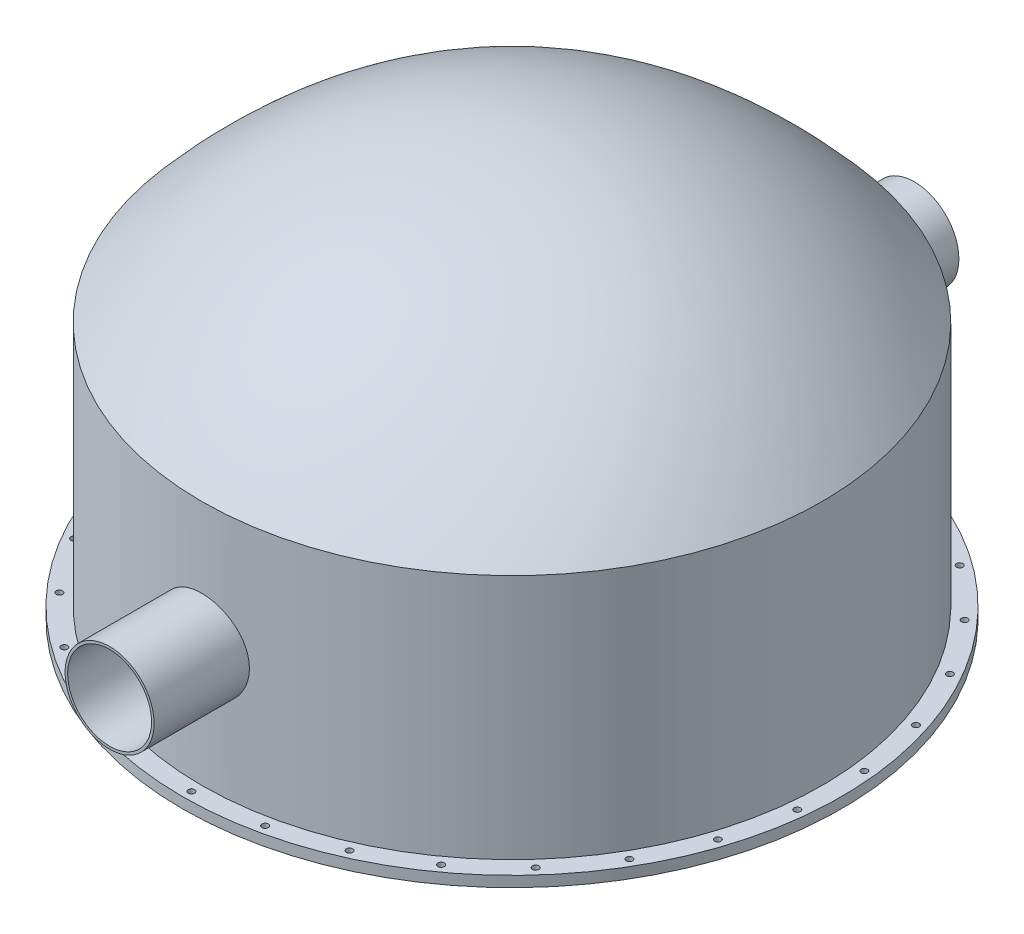
SolidWorks part; units mm, degrees
ref_plane "Front Plane" through (0, 0, 0) normal (0, 0, 1) x (1, 0, 0)
ref_plane "Top Plane" through (0, 0, 0) normal (0, 1, 0) x (1, 0, 0)
ref_plane "Right Plane" through (0, 0, 0) normal (1, 0, 0) x (0, 0, -1)
sketch "Sketch1" plane through (0, 0, 0) normal (1, 0, 0) x (0, 0, -1)
  line L0 (0, 1298.8176) -> (0, 0) construction
  line L1 (0, 0) -> (2076.3065, 0) construction
  line L2 (-2081.13, 0) -> (-2081.13, -1741.115)
  line L3 (-931.3985, 1044.41) -> (931.3985, 1044.41) construction
  line L4 (-2126.02, 16.9087) -> (-2126.02, -1668.115)
  line L5 (-2081.13, -1741.115) -> (-2258.02, -1741.115)
  line L6 (-2258.02, -1741.115) -> (-2258.02, -1668.115)
  line L7 (-2258.02, -1668.115) -> (-2126.02, -1668.115)
  line L8 (0, 1089.3) -> (0, 1044.41)
  line L9 (-2126.02, 16.9087) -> (-2126.02, -1741.115) construction
  spline S0 degree 2 poles (0, 1044.41) (-1164.2481, 1044.41) (-2081.13, 0) knots 0 0 0 1 1 1
  spline S1 degree 1 poles (0, 1089.3) (-2126.02, 16.9087) knots 0 0 1 1 construction
  spline S2 degree 2 poles (0, 1089.3) (-223.4621, 1089.3111) (-581.4225, 1026.2119) (-859.8109, 942.0722) (-1130.0194, 824.365) (-1391.8992, 673.2353) (-1613.6933, 511.8966) (-1768.177, 381.1304) (-1874.4808, 282.365) (-1949.432, 207.9512) (-2001.4413, 154.0583) (-2038.3467, 114.598) (-2064.0667, 86.5254) (-2082.3772, 66.2322) (-2095.1661, 51.9146) (-2104.2861, 41.627) (-2110.6619, 34.3993) (-2115.2157, 29.2163) (-2121.5106, 22.0449) (-2126.02, 16.9087) knots 0 0 0 0.188641 0.314401 0.440161 0.565922 0.691682 0.786003 0.848883 0.896043 0.927483 0.951063 0.966783 0.978573 0.986433 0.992328 0.996258 0.999206 1.001171 1.006083 1.006083 1.006083
  point P15 (0, 0)
  point P16 (0, 0)
  dimension "D1" = 1044.41
  dimension "D2" = 2081.13
  dimension "D3" = 1741.115
  dimension "D5" = 132
  dimension "D6" = 73
  dimension "D4" = 44.89
revolve "Revolve1" add sketch "Sketch1" angle 360 about L0
ref_plane "Plane1" through (0, 0, 2757) normal (0, 0, 1) x (1, 0, 0)
sketch "Sketch3" plane through (0, 0, 2757) normal (0, 0, 1) x (1, 0, 0)
  line L0 (-2258.02, -1741.115) -> (2258.02, -1741.115) construction
  circle A0 centre (0, -832.615) radius 304.8
  dimension "D1" = 609.6
  dimension "D2" = 908.5
extrude "Boss-Extrude1" add sketch "Sketch3" against normal up to surface
mirror "Mirror1" about plane through (0, 0, 0) normal (0, 0, 1) of "Boss-Extrude1"
sketch "Sketch4" plane through (0, 0, 2757) normal (0, 0, 1) x (1, 0, 0)
  circle A0 centre (0, -832.615) radius 287.4
extrude "Cut-Extrude1" cut sketch "Sketch4" against normal through all
sketch "Sketch5" plane through (0, -1741.115, 0) normal (0, -1, 0) x (1, 0, 0)
  circle A0 centre (0, 0) radius 2196.0235 construction
  circle A1 centre (0, 2196.0235) radius 22
  circle A2 centre (456.579, 2148.0351) radius 22
  circle A3 centre (893.2032, 2006.1673) radius 22
  circle A4 centre (1290.7902, 1776.6203) radius 22
  circle A5 centre (1631.9635, 1469.4265) radius 22
  circle A6 centre (1901.8121, 1098.0118) radius 22
  circle A7 centre (2088.5425, 678.6086) radius 22
  circle A8 centre (2183.9935, 229.547) radius 22
  circle A9 centre (2183.9935, -229.547) radius 22
  circle A10 centre (2088.5425, -678.6086) radius 22
  circle A11 centre (1901.8121, -1098.0117) radius 22
  circle A12 centre (1631.9635, -1469.4265) radius 22
  circle A13 centre (1290.7902, -1776.6203) radius 22
  circle A14 centre (893.2032, -2006.1673) radius 22
  circle A15 centre (456.579, -2148.0351) radius 22
  circle A16 centre (0, -2196.0235) radius 22
  circle A17 centre (-456.579, -2148.0351) radius 22
  circle A18 centre (-893.2032, -2006.1673) radius 22
  circle A19 centre (-1290.7902, -1776.6203) radius 22
  circle A20 centre (-1631.9635, -1469.4265) radius 22
  circle A21 centre (-1901.8121, -1098.0118) radius 22
  circle A22 centre (-2088.5425, -678.6086) radius 22
  circle A23 centre (-2183.9935, -229.547) radius 22
  circle A24 centre (-2183.9935, 229.547) radius 22
  circle A25 centre (-2088.5425, 678.6086) radius 22
  circle A26 centre (-1901.8121, 1098.0117) radius 22
  circle A27 centre (-1631.9635, 1469.4265) radius 22
  circle A28 centre (-1290.7902, 1776.6203) radius 22
  circle A29 centre (-893.2032, 2006.1673) radius 22
  circle A30 centre (-456.579, 2148.0351) radius 22
  point P66 (0, 0)
  dimension "D1" = 30
extrude "Cut-Extrude2" cut sketch "Sketch5" against normal up to next (73 mm away)
